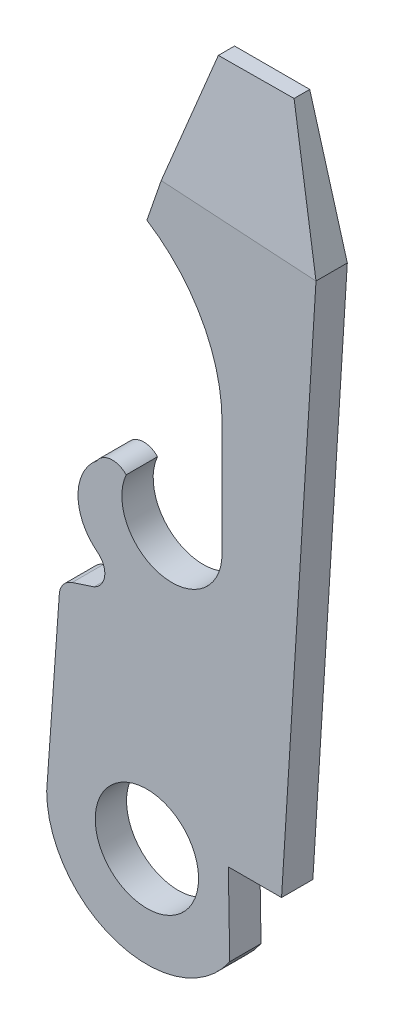
SolidWorks part; units mm, degrees
material "Plain Carbon Steel"
ref_plane "Front Plane" through (0, 0, 0) normal (0, 0, 1) x (1, 0, 0)
ref_plane "Top Plane" through (0, 0, 0) normal (0, 1, 0) x (1, 0, 0)
ref_plane "Right Plane" through (0, 0, 0) normal (1, 0, 0) x (0, 0, -1)
sketch "Sketch1" plane through (0, 0, 0) normal (0, 0, 1) x (1, 0, 0)
  line L0 (14.7211, 33.1224) -> (73.6054, 33.1224) construction
  line L1 (48.6367, 40.0161) -> (47.2397, 17.6641)
  line L2 (47.2397, 17.6641) -> (45.0807, 17.6641)
  line L3 (44.0647, 45.3501) -> (47.1127, 45.3501)
  line L4 (47.1127, 45.3501) -> (48.6367, 40.0161)
  line L5 (44.0647, 45.3501) -> (41.7787, 38.7229)
  line L6 (44.8267, 33.1581) -> (44.8267, 28.5353)
  line L7 (45.0807, 17.6641) -> (45.1388, 14.3621)
  line L8 (38.2227, 23.7601) -> (37.7147, 16.6481)
  line L9 (38.7469, 24.484) -> (39.6358, 24.7761)
  arc A1 (40.938, 29.3608) -> (44.8267, 28.5353) centre (42.7947, 28.5353) ccw
  arc A2 (39.742, 29.2541) -> (39.7769, 26.0617) centre (41.0167, 27.6717) ccw
  arc A3 (40.938, 29.3608) -> (39.742, 29.2541) centre (40.3817, 28.8401) ccw
  arc A4 (39.6358, 24.7761) -> (39.7769, 26.0617) centre (39.3149, 25.4619) ccw
  arc A5 (38.7469, 24.484) -> (38.2227, 23.7601) centre (38.9847, 23.7601) ccw
  arc A6 (37.7147, 16.6481) -> (45.1388, 14.3621) centre (41.7787, 16.6481) ccw
  arc A7 (44.8267, 33.1581) -> (41.7787, 38.7229) centre (38.2227, 33.1581) ccw
  point P22 (0, 0)
  dimension "D6" = 2.286
  dimension "D7" = 23.368
  dimension "D8" = 6.858
  dimension "D9" = 5.461
  dimension "D10" = 28.702
  dimension "D11" = 5.334
  dimension "D13" = 16.51
  dimension "D16" = 11.8872
  dimension "D18" = 2.032
  dimension "D21" = 1.397
  dimension "D24" = 2.032
  dimension "D1" = 4.064
  dimension "D15" = 6.604
  dimension "D19" = 0.762
  dimension "D2" = 3.556
  dimension "D3" = 7.112
  dimension "D4" = 1.016
  dimension "D5" = 3.302
  dimension "D12" = 2.286
  dimension "D14" = 3.556
  dimension "D17" = 1.016
  dimension "D20" = 12.192
  dimension "D22" = 11.0236
  dimension "D23" = 0.762
  dimension "D25" = 8.8138
  dimension "D26" = 2.4638
  dimension "D27" = 2.794
  dimension "D28" = 8.128
extrude "Boss-Extrude1" add sketch "Sketch1" along normal blind 1.27
sketch "Sketch2" plane through (0, 0, 1.27) normal (0, 0, 1) x (1, 0, 0)
  circle A0 centre (41.7787, 16.6481) radius 2.0955
  dimension "D1" = 4.191
extrude "Cut-Extrude1" cut sketch "Sketch2" against normal through all
sketch "Sketch3" plane through (45.9562, -2.8723, 0) normal (0.9981, -0.0624, 0) x (0, 0, -1)
  line L2 (-0.635, 48.2006) -> (-1.27, 42.972)
  line L3 (-1.27, 42.972) -> (-1.27, 48.2006)
  line L4 (-1.27, 48.2006) -> (-0.635, 48.2006)
  dimension "D1" = 0.635
extrude "Cut-Extrude2" cut sketch "Sketch3" against normal through all
